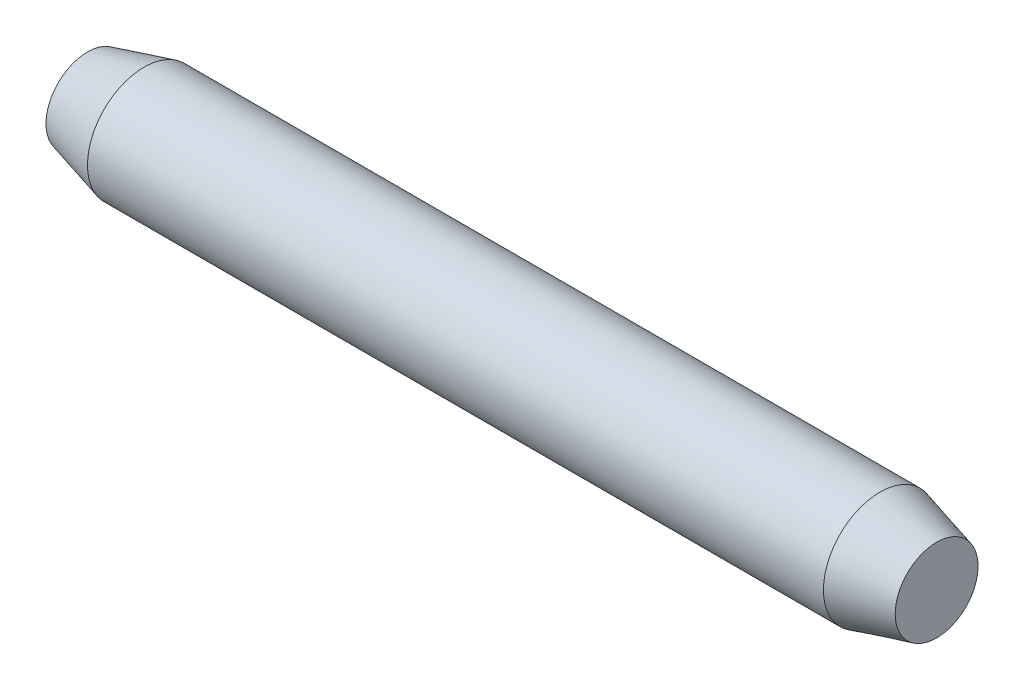
SolidWorks part; units mm, degrees
ref_plane "Plane1" through (0, 0, 0) normal (0, 0, 1) x (1, 0, 0)
ref_plane "Plane2" through (0, 0, 0) normal (0, 1, 0) x (1, 0, 0)
ref_plane "Plane3" through (0, 0, 0) normal (1, 0, 0) x (0, 0, -1)
sketch "Sketch1" plane through (0, 0, 0) normal (0, 0, 1) x (1, 0, 0)
  line L1 (-6.35, 0) -> (107.95, 0) construction
  line L2 (0, 0) -> (15, 0)
  line L3 (15, 0) -> (15, 0.7321)
  line L4 (15, 0.7321) -> (14, 1)
  line L5 (14, 1) -> (1, 1)
  line L6 (0, 0.7321) -> (0, 0)
  line L7 (0, 0.7321) -> (1, 1)
  dimension "D1" = 1
  dimension "D2" = 15
  dimension "D3" = 15
  dimension "Diameter" = 2
  dimension "Length" = 15
  dimension "Chamfer_len" = 1
revolve "Base-Revolve" add sketch "Sketch1" angle 360 about L1
equation "\"D3@Sketch1\" = 15.0"
equation "\"D1@Sketch1\" = \"Chamfer_len@Sketch1\""
equation "\"D2@Sketch1\" = \"D3@Sketch1\""
